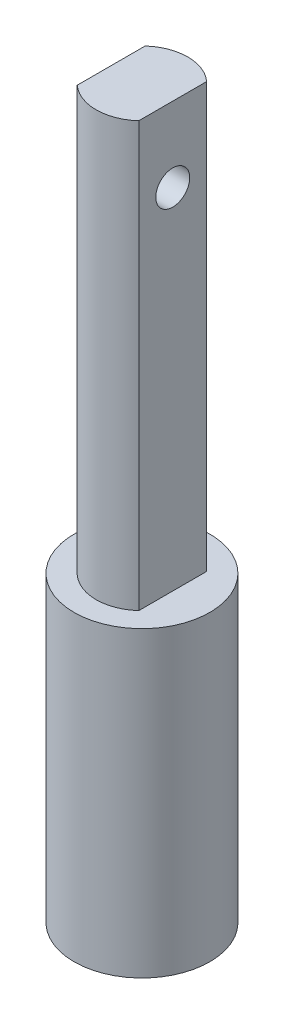
SolidWorks part; units mm, degrees
ref_plane "Front Plane" through (0, 0, 0) normal (0, 0, 1) x (1, 0, 0)
ref_plane "Top Plane" through (0, 0, 0) normal (0, 1, 0) x (1, 0, 0)
ref_plane "Right Plane" through (0, 0, 0) normal (1, 0, 0) x (0, 0, -1)
sketch "Sketch1" plane through (0, 0, 0) normal (0, 1, 0) x (1, 0, 0)
  line L0 (-2, 1.8875) -> (2, 1.8875)
  line L1 (-2.9341, 0) -> (3.2052, 0) construction
  line L2 (-2, -1.8875) -> (2, -1.8875)
  arc A0 (-2, 1.8875) -> (-2, -1.8875) centre (0, 0) ccw
  circle A1 centre (0, 0) radius 4
  arc A2 (2, -1.8875) -> (2, 1.8875) centre (0, 0) ccw
  dimension "D1" = 4
  dimension "D2" = 2.75
  dimension "D3" = 8
extrude "Boss-Extrude1" add sketch "Sketch1" along normal blind 9
sketch "Sketch2" plane through (0, 9, 0) normal (0, 1, 0) x (1, 0, 0)
  circle A0 centre (0, 0) radius 4
extrude "Boss-Extrude2" add sketch "Sketch2" along normal blind 8.83
sketch "Sketch3" plane through (0, 17.83, 0) normal (0, 1, 0) x (1, 0, 0)
  line L0 (1.8138, 2) -> (1.8138, -2)
  line L1 (0, 2.6412) -> (0, -2.8621) construction
  line L2 (-1.8138, 2) -> (-1.8138, -2)
  arc A0 (1.8138, 2) -> (-1.8138, 2) centre (0, 0) ccw
  arc A1 (-1.8138, -2) -> (1.8138, -2) centre (0, 0) ccw
  dimension "D1" = 2.7
  dimension "D2" = 4
extrude "Boss-Extrude3" add sketch "Sketch3" along normal blind 25
sketch "Sketch4" plane through (1.8138, 0, 0) normal (1, 0, 0) x (0, 0, -1)
  circle A0 centre (0, 38.4218) radius 1
  point P2 (0, 38.4218)
extrude "Cut-Extrude1" cut sketch "Sketch4" against normal blind 25
